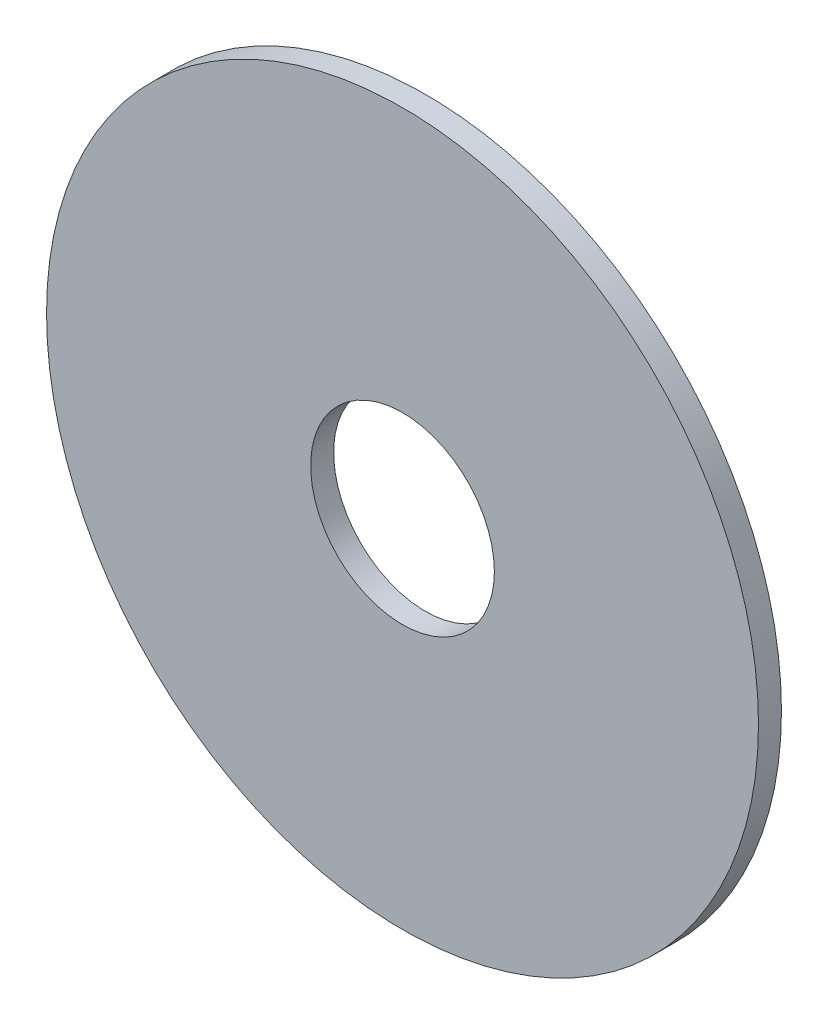
SolidWorks part; units mm, degrees
ref_plane "Front Plane" through (0, 0, 0) normal (0, 0, 1) x (1, 0, 0)
ref_plane "Top Plane" through (0, 0, 0) normal (0, 1, 0) x (1, 0, 0)
ref_plane "Right Plane" through (0, 0, 0) normal (1, 0, 0) x (0, 0, -1)
sketch "Croquis1" plane through (0, 0, 0) normal (0, 0, 1) x (1, 0, 0)
  circle A0 centre (0, 0) radius 3.875
  circle A1 centre (0, 0) radius 1
  dimension "D1" = 7.75
  dimension "D2" = 2
extrude "Saliente-Extruir1" add sketch "Croquis1" along normal blind 0.25
